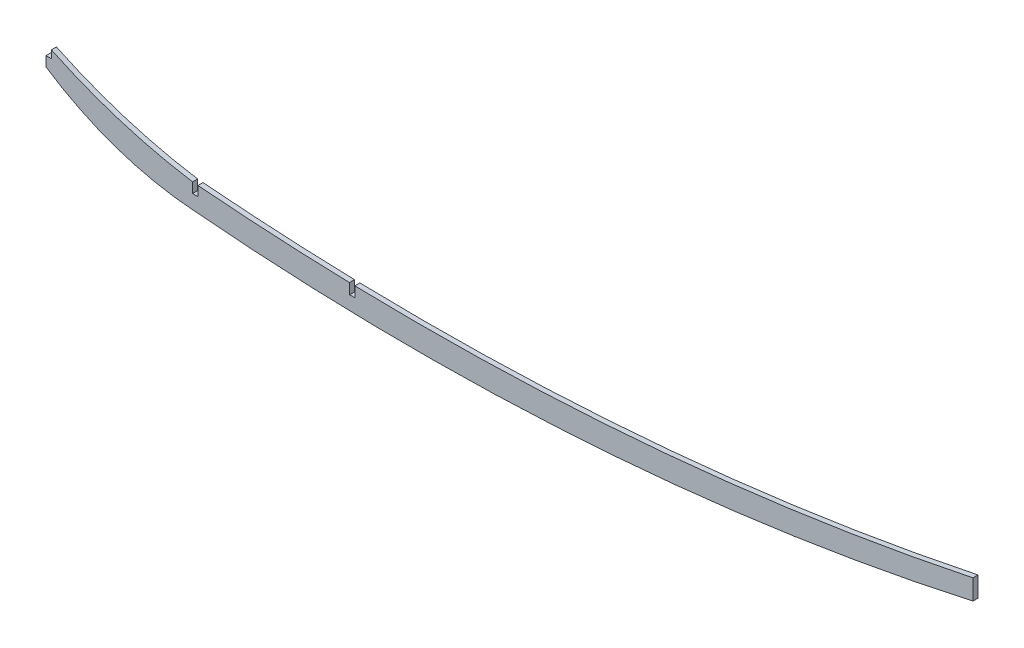
SolidWorks part; units mm, degrees
material "Plywood"
ref_plane "Front Plane" through (0, 0, 0) normal (0, 0, 1) x (1, 0, 0)
ref_plane "Top Plane" through (0, 0, 0) normal (0, 1, 0) x (1, 0, 0)
ref_plane "Right Plane" through (0, 0, 0) normal (1, 0, 0) x (0, 0, -1)
sketch "Sketch1" plane through (0, 0, 0) normal (0, 0, 1) x (1, 0, 0)
  line L3 (0, -97.563) -> (0, -84.863)
  line L4 (583.5225, -97.0036) -> (583.5225, -84.3036)
  arc A6 (0, -97.563) -> (92.3925, -129.289) centre (106.9176, 63.4069) ccw
  arc A10 (92.3925, -129.289) -> (583.5225, -97.0036) centre (233.5795, 1474.6667) ccw
  arc A17 (0, -84.863) -> (92.3925, -114.049) centre (142.0237, 203.9001) ccw
  arc A19 (92.3925, -114.049) -> (583.5225, -84.3036) centre (236.5524, 1575.136) ccw
  dimension "D1" = 193.2426
  dimension "D5" = 1610.1576
  dimension "D6" = 583.5225
  dimension "D4" = 31.726
  dimension "D10" = 15.24
  dimension "D11" = 321.7994
  dimension "D12" = 1695.3253
  dimension "D2" = 97.563
  dimension "D3" = 92.3925
  dimension "D7" = 97.0036
  dimension "D8" = 12.7
  dimension "D9" = 12.7
extrude "Boss-Extrude1" add sketch "Sketch1" along normal mid plane 3.175
sketch "Sketch2" plane through (0, 0, 1.5875) normal (0, 0, 1) x (1, 0, 0)
  line L0 (0, 0) -> (0, -84.863) construction
  line L1 (0, 0) -> (93.98, 0) construction
  line L2 (0, -84.863) -> (3.3782, -84.863)
  line L3 (0, -84.863) -> (0, -91.34)
  line L4 (0, -91.34) -> (3.3782, -91.34)
  line L5 (3.3782, -84.863) -> (3.3782, -91.34)
  line L6 (93.98, 0) -> (93.98, -120.3396) construction
  line L9 (92.2909, -120.4158) -> (95.6691, -120.4158)
  line L10 (92.2909, -120.4158) -> (92.2909, -107.7158)
  line L11 (95.6691, -120.4158) -> (95.6691, -107.7158)
  line L12 (92.2909, -107.7158) -> (95.6691, -107.7158)
  line L14 (191.1554, -126.1955) -> (194.5328, -126.1248)
  line L21 (192.8425, -126.084) -> (190.203, 0) construction
  line L23 (93.98, 0) -> (241.3865, 0) construction
  line L25 (191.1554, -126.1955) -> (190.8896, -113.4983)
  line L26 (194.5328, -126.1248) -> (194.267, -113.4276)
  line L27 (190.8896, -113.4983) -> (194.267, -113.4276)
  point P3 (93.98, -107.7158)
  point P11 (192.5783, -113.463)
  point P14 (192.8441, -126.1602)
  dimension "D1" = 84.863
  dimension "D2" = 6.477
  dimension "D3" = 3.3782
  dimension "D4" = 93.98
  dimension "D5" = 120.3396
  dimension "D6" = 0.0762
  dimension "D7" = 3.3782
  dimension "D8" = 91.199
  dimension "D9" = 190.203
  dimension "D10" = 126.1116
  dimension "D11" = 0.0762
  dimension "D12" = 3.3782
  dimension "D13" = 12.7
  dimension "D14" = 12.7
extrude "Cut-Extrude1" cut sketch "Sketch2" against normal through all
equation "\"slotwidth\"=0.197118"
